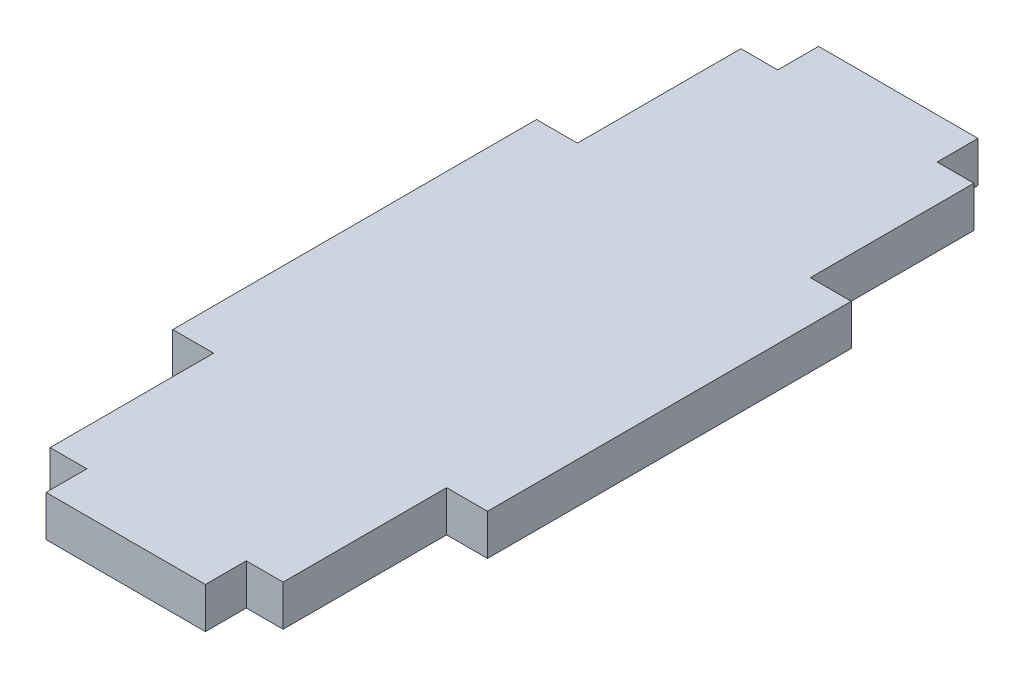
SolidWorks part; units mm, degrees
ref_plane "Front Plane" through (0, 0, 0) normal (0, 0, 1) x (1, 0, 0)
ref_plane "Top Plane" through (0, 0, 0) normal (0, 1, 0) x (1, 0, 0)
ref_plane "Right Plane" through (0, 0, 0) normal (1, 0, 0) x (0, 0, -1)
sketch "Sketch1" plane through (0, 0, 0) normal (0, 1, 0) x (1, 0, 0)
  line L0 (0, 73.3247) -> (0, -83.4245) construction
  line L5 (-14.25, 42.25) -> (-9.75, 42.25)
  line L11 (-14.25, 42.25) -> (-14.25, 22.25)
  line L12 (-14.25, -42.25) -> (-9.75, -42.25)
  line L23 (9.75, -47.25) -> (9.75, -42.25)
  line L24 (-9.75, -47.25) -> (9.75, -47.25)
  line L30 (14.25, 42.25) -> (14.25, 22.25)
  line L31 (-73.9307, 0) -> (122.6118, 0) construction
  line L32 (-9.75, 42.25) -> (-9.75, 47.25)
  line L33 (-9.75, 47.25) -> (9.75, 47.25)
  line L34 (9.75, 47.25) -> (9.75, 42.25)
  line L35 (-14.25, 22.25) -> (-19.25, 22.25)
  line L36 (-19.25, 22.25) -> (-19.25, -22.25)
  line L37 (-19.25, -22.25) -> (-14.25, -22.25)
  line L38 (-14.25, -22.25) -> (-14.25, -42.25)
  line L39 (-14.25, 22.25) -> (-14.25, 0) construction
  line L40 (-14.25, 0) -> (-14.25, -22.25) construction
  line L41 (9.75, 42.25) -> (14.25, 42.25)
  line L42 (-9.75, 42.25) -> (0, 42.25) construction
  line L43 (0, 42.25) -> (9.75, 42.25) construction
  line L44 (19.25, -22.25) -> (14.25, -22.25)
  line L45 (19.25, 22.25) -> (19.25, -22.25)
  line L46 (14.25, 22.25) -> (19.25, 22.25)
  line L47 (-9.75, -42.25) -> (-9.75, -47.25)
  line L48 (14.25, -22.25) -> (14.25, -42.25)
  line L49 (14.25, 22.25) -> (14.25, 0) construction
  line L50 (14.25, 0) -> (14.25, -22.25) construction
  line L51 (9.75, -42.25) -> (14.25, -42.25)
  line L52 (0, -42.25) -> (9.75, -42.25) construction
  line L53 (-9.75, -42.25) -> (0, -42.25) construction
  dimension "D1" = 84.5
  dimension "D2" = 28.5
  dimension "D3" = 5
  dimension "D4" = 5
  dimension "D5" = 19.5
  dimension "D6" = 44.5
  dimension "D7" = 38.5
extrude "Boss-Extrude1" add sketch "Sketch1" along normal blind 5
